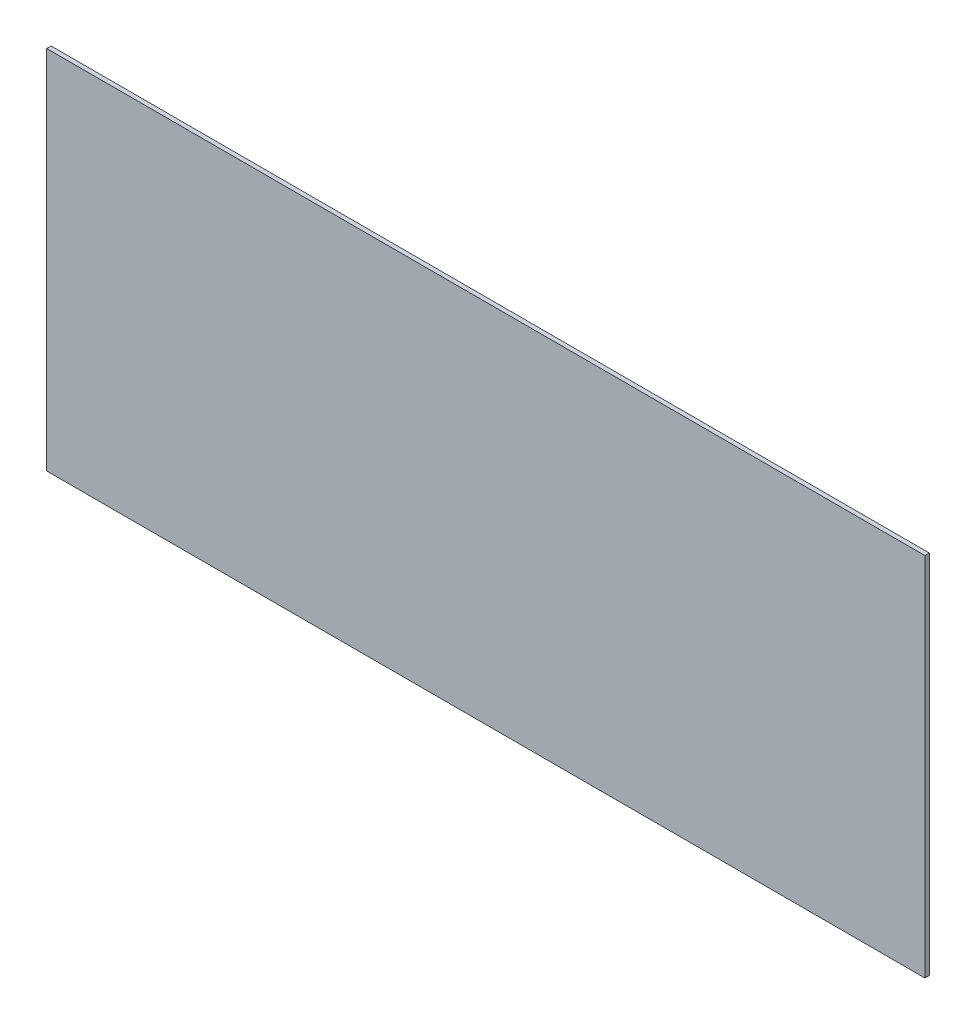
SolidWorks part; units mm, degrees
ref_plane "정면" through (0, 0, 0) normal (0, 0, 1) x (1, 0, 0)
ref_plane "윗면" through (0, 0, 0) normal (0, 1, 0) x (1, 0, 0)
ref_plane "우측면" through (0, 0, 0) normal (1, 0, 0) x (0, 0, -1)
sketch "스케치1" plane through (0, 0, 0) normal (0, 1, 0) x (1, 0, 0)
  line L1 (0, 0) -> (600, 0)
  line L2 (0, 0) -> (0, 3)
  line L3 (0, 3) -> (600, 3)
  line L4 (600, 0) -> (600, 3)
  dimension "D1" = 3
  dimension "D2" = 600
extrude "보스-돌출1" add sketch "스케치1" along normal blind 250
